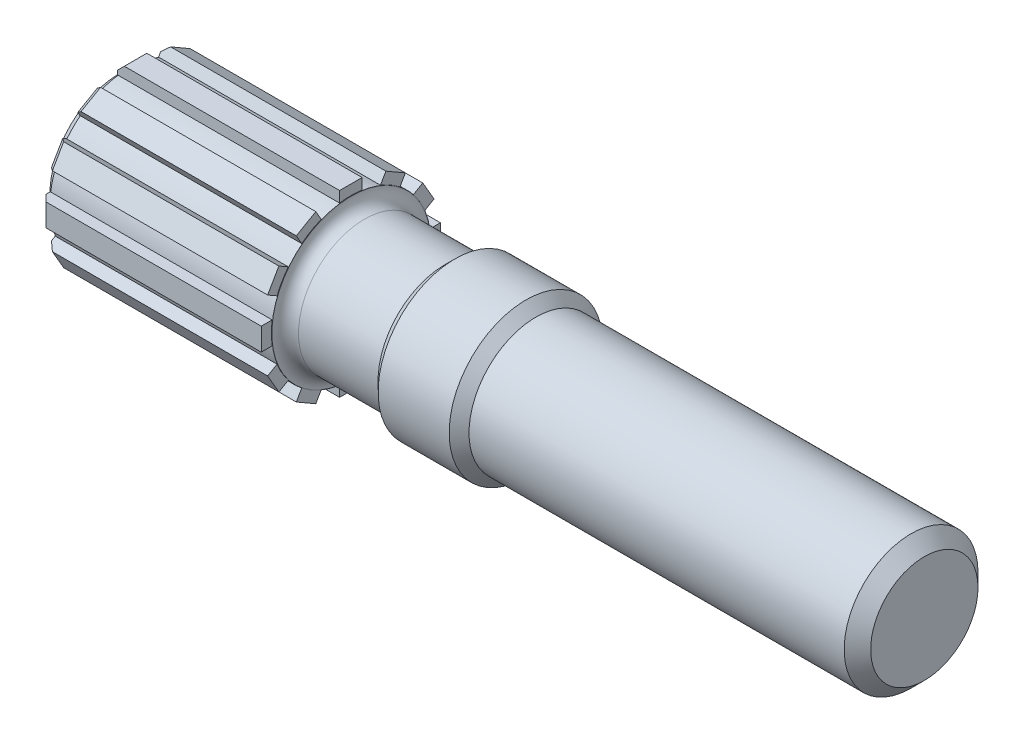
SolidWorks part; units mm, degrees
ref_plane "Front Plane" through (0, 0, 0) normal (0, 0, 1) x (1, 0, 0)
ref_plane "Top Plane" through (0, 0, 0) normal (0, 1, 0) x (1, 0, 0)
ref_plane "Right Plane" through (0, 0, 0) normal (1, 0, 0) x (0, 0, -1)
sketch "Sketch1" plane through (0, 0, 0) normal (0, 1, 0) x (1, 0, 0)
  line L0 (77.9948, 0) -> (-59.5052, 0) construction
  line L2 (-44.8637, 0) -> (76.6649, 0)
  line L3 (-44.8637, 10.5) -> (-44.8637, 0)
  line L4 (16.5246, 11.6037) -> (5.8003, 11.6037)
  line L5 (76.6649, 0) -> (76.6649, 8.1029)
  line L6 (-9.8637, 11.9623) -> (-9.8637, 12)
  line L8 (-43.3637, 12) -> (-9.8637, 12)
  line L9 (-7.8637, 9.9623) -> (4.3003, 9.9623)
  line L10 (18.0246, 10.1029) -> (74.6649, 10.1029)
  line L11 (4.3003, 9.9623) -> (4.3003, 10.1037)
  line L12 (74.6649, 10.1029) -> (76.6649, 8.1029)
  line L13 (5.8003, 11.6037) -> (4.3003, 10.1037)
  line L14 (18.0246, 10.1029) -> (18.0246, 10.1037)
  line L15 (18.0246, 10.1037) -> (16.5246, 11.6037)
  line L16 (-44.8637, 10.5) -> (-43.3637, 12)
  arc A0 (-7.8637, 9.9623) -> (-9.8637, 11.9623) centre (-7.8637, 11.9623) cw
  point P4 (76.6649, 10.1029)
  point P8 (-44.8637, 12)
  point P13 (4.3003, 11.6037)
  point P14 (-44.8637, 12)
  point P23 (18.0246, 11.6037)
  dimension "D3" = 2
  dimension "D1" = 24
  dimension "D2" = 35
revolve "Revolve1" add sketch "Sketch1" angle 360 about L0
sketch "Sketch2" plane through (-44.9219, 0, 0) normal (-1, 0, 0) x (0, 0, 1)
  line L2 (-1.6992, 13.5246) -> (1.6992, 13.5246)
  line L3 (-1.6992, 13.5246) -> (-1.6992, 11.0856)
  line L4 (-1.6992, 11.0856) -> (1.6992, 11.0856)
  line L5 (1.6992, 13.5246) -> (1.6992, 11.0856)
  point P0 (0, 13.5246)
  point P3 (0, 0)
  dimension "D1" = 3.3984
  dimension "D2" = 13.5246
extrude "Boss-Extrude1" add sketch "Sketch2" against normal blind 33.5 from offset 1.5 offset against normal yes
pattern_circular "CirPattern1" count 12 over 360 about axis through (0, 0, 0) along (1, 0, 0) of "Boss-Extrude1"
chamfer "Chamfer1" distance 1 angle 45 12 edges at (-43.4219, 11.7127, 6.7623) (-43.4219, 6.7623, 11.7127) (-43.4219, 0, 13.5246) (-43.4219, -6.7623, 11.7127) (-43.4219, -11.7127, 6.7623) (-43.4219, -13.5246, 0) (-43.4219, -11.7127, -6.7623) (-43.4219, -6.7623, -11.7127) (-43.4219, 0, -13.5246) (-43.4219, 6.7623, -11.7127) (-43.4219, 11.7127, -6.7623) (-43.4219, 13.5246, 0)
